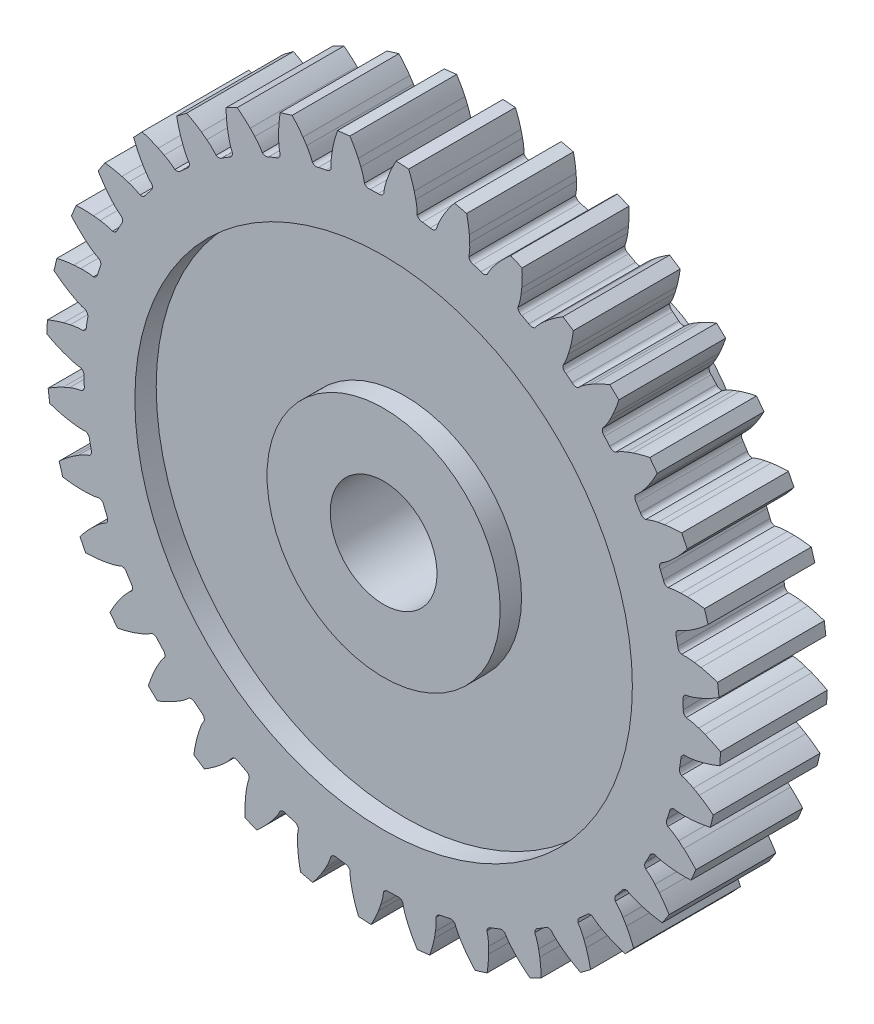
SolidWorks part; units mm, degrees
ref_plane "Front Plane" through (0, 0, 0) normal (0, 0, 1) x (1, 0, 0)
ref_plane "Top Plane" through (0, 0, 0) normal (0, 1, 0) x (1, 0, 0)
ref_plane "Right Plane" through (0, 0, 0) normal (1, 0, 0) x (0, 0, -1)
sketch "Model" plane through (0, 0, 0) normal (0, 0, 1) x (1, 0, 0)
  line L0 (77.4091, 88.3835) -> (77.6633, 88.6903)
  line L1 (78.392, 89.4098) -> (79.0739, 89.1177)
  line L2 (79.0555, 88.0937) -> (79.0087, 87.6981)
  line L3 (79.0512, 86.6569) -> (79.4656, 86.4348)
  line L4 (80.3562, 86.9756) -> (80.6598, 87.2336)
  line L5 (81.5024, 87.8157) -> (82.1232, 87.4096)
  line L6 (81.9273, 86.4044) -> (81.8124, 86.0229)
  line L7 (81.6735, 84.9902) -> (82.0431, 84.6994)
  line L8 (83.0141, 85.0774) -> (83.3578, 85.2788)
  line L9 (84.2887, 85.7057) -> (84.8295, 85.198)
  line L10 (84.462, 84.242) -> (84.2827, 83.8863)
  line L11 (83.9666, 82.8934) -> (84.28, 82.5429)
  line L12 (85.3019, 82.7465) -> (85.6754, 82.8851)
  line L13 (86.6663, 83.144) -> (87.1107, 82.55)
  line L14 (86.5828, 81.6724) -> (86.3444, 81.3532)
  line L15 (85.8607, 80.4303) -> (86.1085, 80.0307)
  line L16 (87.1503, 80.0538) -> (87.5422, 80.1254)
  line L17 (88.5629, 80.2082) -> (88.8975, 79.5461)
  line L18 (88.2252, 78.7735) -> (87.935, 78.5006)
  line L19 (87.2984, 77.6757) -> (87.473, 77.2391)
  line L20 (88.5029, 77.0809) -> (88.9013, 77.0835)
  line L21 (89.921, 76.9878) -> (90.1354, 76.2776)
  line L22 (89.3392, 75.6335) -> (89.006, 75.4151)
  line L23 (88.2358, 74.7133) -> (88.332, 74.253)
  line L24 (89.3188, 73.9184) -> (89.7116, 73.8517)
  line L25 (90.6991, 73.5804) -> (90.787, 72.8438)
  line L26 (89.891, 72.3477) -> (89.525, 72.1905)
  line L27 (88.6446, 71.6331) -> (88.6594, 71.1631)
  line L28 (89.5731, 70.6623) -> (89.9484, 70.5284)
  line L29 (90.8738, 70.0897) -> (90.8324, 69.349)
  line L30 (89.8639, 69.0161) -> (89.4761, 68.9248)
  line L31 (88.5123, 68.5287) -> (88.4453, 68.0633)
  line L32 (89.2582, 67.4114) -> (89.6044, 67.2144)
  line L33 (90.4396, 66.6217) -> (90.2703, 65.8994)
  line L34 (89.2587, 65.7397) -> (88.8609, 65.7172)
  line L35 (87.843, 65.4945) -> (87.6962, 65.0478)
  line L36 (88.3835, 64.2646) -> (88.6903, 64.0105)
  line L37 (89.4099, 63.2817) -> (89.1177, 62.5999)
  line L38 (88.0937, 62.6183) -> (87.6981, 62.6651)
  line L39 (86.6569, 62.6226) -> (86.4348, 62.2082)
  line L40 (86.9756, 61.3175) -> (87.2336, 61.014)
  line L41 (87.8157, 60.1714) -> (87.4096, 59.5506)
  line L42 (86.4044, 59.7465) -> (86.0229, 59.8614)
  line L43 (84.9902, 60.0002) -> (84.6995, 59.6307)
  line L44 (85.0774, 58.6597) -> (85.2788, 58.3159)
  line L45 (85.7058, 57.385) -> (85.198, 56.8442)
  line L46 (84.2421, 57.2117) -> (83.8863, 57.3911)
  line L47 (82.8934, 57.7072) -> (82.5429, 57.3938)
  line L48 (82.7465, 56.3719) -> (82.8852, 55.9983)
  line L49 (83.144, 55.0075) -> (82.55, 54.563)
  line L50 (81.6724, 55.0909) -> (81.3532, 55.3293)
  line L51 (80.4303, 55.8131) -> (80.0307, 55.5653)
  line L52 (80.0538, 54.5235) -> (80.1254, 54.1316)
  line L53 (80.2082, 53.1108) -> (79.5461, 52.7763)
  line L54 (78.7735, 53.4486) -> (78.5006, 53.7388)
  line L55 (77.6757, 54.3754) -> (77.2391, 54.2008)
  line L56 (77.081, 53.1709) -> (77.0835, 52.7725)
  line L57 (76.9878, 51.7528) -> (76.2776, 51.5383)
  line L58 (75.6335, 52.3346) -> (75.4151, 52.6678)
  line L59 (74.7133, 53.438) -> (74.253, 53.3418)
  line L60 (73.9184, 52.355) -> (73.8517, 51.9622)
  line L61 (73.5804, 50.9746) -> (72.8438, 50.8868)
  line L62 (72.3478, 51.7827) -> (72.1905, 52.1488)
  line L63 (71.6331, 53.0292) -> (71.1632, 53.0144)
  line L64 (70.6623, 52.1006) -> (70.5284, 51.7254)
  line L65 (70.0897, 50.8) -> (69.349, 50.8413)
  line L66 (69.0161, 51.8098) -> (68.9248, 52.1977)
  line L67 (68.5287, 53.1614) -> (68.0633, 53.2285)
  line L68 (67.4114, 52.4156) -> (67.2144, 52.0693)
  line L69 (66.6217, 51.2341) -> (65.8994, 51.4035)
  line L70 (65.7397, 52.4151) -> (65.7172, 52.8129)
  line L71 (65.4945, 53.8308) -> (65.0478, 53.9776)
  line L72 (64.2646, 53.2903) -> (64.0105, 52.9835)
  line L73 (63.2817, 52.2639) -> (62.5999, 52.5561)
  line L74 (62.6183, 53.5801) -> (62.6651, 53.9757)
  line L75 (62.6226, 55.0168) -> (62.2082, 55.239)
  line L76 (61.3175, 54.6981) -> (61.014, 54.4401)
  line L77 (60.1714, 53.858) -> (59.5506, 54.2642)
  line L78 (59.7465, 55.2694) -> (59.8614, 55.6509)
  line L79 (60.0002, 56.6836) -> (59.6307, 56.9743)
  line L80 (58.6597, 56.5963) -> (58.3159, 56.395)
  line L81 (57.385, 55.968) -> (56.8442, 56.4758)
  line L82 (57.2117, 57.4317) -> (57.3911, 57.7875)
  line L83 (57.7072, 58.7804) -> (57.3938, 59.1308)
  line L84 (56.3719, 58.9272) -> (55.9983, 58.7886)
  line L85 (55.0075, 58.5298) -> (54.563, 59.1238)
  line L86 (55.0909, 60.0013) -> (55.3293, 60.3206)
  line L87 (55.8131, 61.2435) -> (55.5653, 61.6431)
  line L88 (54.5235, 61.62) -> (54.1316, 61.5483)
  line L89 (53.1108, 61.4655) -> (52.7763, 62.1276)
  line L90 (53.4486, 62.9002) -> (53.7388, 63.1732)
  line L91 (54.3754, 63.9981) -> (54.2008, 64.4346)
  line L92 (53.1709, 64.5928) -> (52.7725, 64.5903)
  line L93 (51.7528, 64.686) -> (51.5384, 65.3961)
  line L94 (52.3346, 66.0402) -> (52.6678, 66.2587)
  line L95 (53.438, 66.9605) -> (53.3418, 67.4207)
  line L96 (52.355, 67.7553) -> (51.9622, 67.822)
  line L97 (50.9747, 68.0933) -> (50.8868, 68.83)
  line L98 (51.7827, 69.326) -> (52.1488, 69.4833)
  line L99 (53.0292, 70.0407) -> (53.0144, 70.5106)
  line L100 (52.1007, 71.0115) -> (51.7254, 71.1454)
  line L101 (50.8, 71.5841) -> (50.8414, 72.3247)
  line L102 (51.8098, 72.6577) -> (52.1977, 72.749)
  line L103 (53.1614, 73.145) -> (53.2285, 73.6104)
  line L104 (52.4156, 74.2624) -> (52.0693, 74.4594)
  line L105 (51.2342, 75.0521) -> (51.4035, 75.7743)
  line L106 (52.4151, 75.934) -> (52.8129, 75.9566)
  line L107 (53.8308, 76.1793) -> (53.9776, 76.626)
  line L108 (53.2903, 77.4091) -> (52.9835, 77.6633)
  line L109 (52.2639, 78.392) -> (52.5561, 79.0739)
  line L110 (53.5801, 79.0555) -> (53.9757, 79.0086)
  line L111 (55.0168, 79.0512) -> (55.239, 79.4656)
  line L112 (54.6981, 80.3562) -> (54.4401, 80.6598)
  line L113 (53.858, 81.5024) -> (54.2642, 82.1232)
  line L114 (55.2694, 81.9272) -> (55.6509, 81.8124)
  line L115 (56.6836, 81.6735) -> (56.9743, 82.043)
  line L116 (56.5963, 83.0141) -> (56.395, 83.3578)
  line L117 (55.968, 84.2887) -> (56.4758, 84.8295)
  line L118 (57.4317, 84.462) -> (57.7875, 84.2827)
  line L119 (58.7804, 83.9666) -> (59.1309, 84.28)
  line L120 (58.9272, 85.3019) -> (58.7886, 85.6754)
  line L121 (58.5298, 86.6663) -> (59.1238, 87.1107)
  line L122 (60.0014, 86.5828) -> (60.3206, 86.3444)
  line L123 (61.2435, 85.8607) -> (61.6431, 86.1085)
  line L124 (61.62, 87.1502) -> (61.5483, 87.5422)
  line L125 (61.4655, 88.5629) -> (62.1277, 88.8974)
  line L126 (62.9002, 88.2252) -> (63.1732, 87.935)
  line L127 (63.9981, 87.2983) -> (64.4346, 87.473)
  line L128 (64.5928, 88.5029) -> (64.5903, 88.9013)
  line L129 (64.686, 89.9209) -> (65.3962, 90.1354)
  line L130 (66.0402, 89.3392) -> (66.2587, 89.006)
  line L131 (66.9605, 88.2358) -> (67.4207, 88.332)
  line L132 (67.7553, 89.3188) -> (67.8221, 89.7116)
  line L133 (68.0934, 90.6991) -> (68.83, 90.787)
  line L134 (69.326, 89.891) -> (69.4833, 89.525)
  line L135 (70.0407, 88.6446) -> (70.5106, 88.6594)
  line L136 (71.0115, 89.5731) -> (71.1454, 89.9483)
  line L137 (71.5841, 90.8738) -> (72.3248, 90.8324)
  line L138 (72.6577, 89.8639) -> (72.749, 89.4761)
  line L139 (73.1451, 88.5123) -> (73.6104, 88.4453)
  line L140 (74.2624, 89.2581) -> (74.4594, 89.6044)
  line L141 (75.0521, 90.4396) -> (75.7743, 90.2703)
  line L142 (75.934, 89.2587) -> (75.9566, 88.8609)
  line L143 (76.1793, 87.843) -> (76.626, 87.6962)
  circle A0 centre (70.8369, 70.8369) radius 3.175
  arc A1 (76.626, 87.6962) -> (76.9961, 87.7414) centre (76.7799, 87.9735) ccw
  arc A2 (77.4091, 88.3835) -> (76.9961, 87.7414) centre (79.8839, 86.3375) ccw
  arc A3 (78.392, 89.4098) -> (77.6633, 88.6903) centre (83.4985, 83.5097) ccw
  arc A4 (79.0555, 88.0937) -> (79.0739, 89.1177) centre (71.2797, 88.7455) ccw
  arc A5 (78.8287, 86.9562) -> (79.0087, 87.6981) centre (75.8203, 88.0788) ccw
  arc A6 (78.8287, 86.9562) -> (79.0512, 86.6569) centre (79.1459, 86.9597) ccw
  arc A7 (79.4656, 86.4348) -> (79.838, 86.4151) centre (79.6654, 86.6812) ccw
  arc A8 (80.3562, 86.9756) -> (79.838, 86.4151) centre (82.4381, 84.531) ccw
  arc A9 (81.5024, 87.8157) -> (80.6598, 87.2336) centre (85.5068, 81.1185) ccw
  arc A10 (81.9273, 86.4044) -> (82.1232, 87.4096) centre (74.3828, 88.3966) ccw
  arc A11 (81.5063, 85.3235) -> (81.8124, 86.0229) centre (78.7386, 86.9515) ccw
  arc A12 (81.5063, 85.3235) -> (81.6735, 84.9902) centre (81.8193, 85.2719) ccw
  arc A13 (82.0431, 84.6994) -> (82.4064, 84.6154) centre (82.2826, 84.9074) ccw
  arc A14 (83.0141, 85.0774) -> (82.4064, 84.6154) centre (84.6399, 82.3084) ccw
  arc A15 (84.2887, 85.7057) -> (83.3578, 85.2788) centre (87.0693, 78.4149) ccw
  arc A16 (84.462, 84.242) -> (84.8295, 85.198) centre (77.3781, 87.5141) ccw
  arc A17 (83.8598, 83.2507) -> (84.2827, 83.8863) centre (81.4169, 85.3345) ccw
  arc A18 (83.8598, 83.2507) -> (83.9666, 82.8934) centre (84.1591, 83.1455) ccw
  arc A19 (84.28, 82.5429) -> (84.6232, 82.397) centre (84.552, 82.7062) ccw
  arc A20 (85.3019, 82.7465) -> (84.6232, 82.397) centre (86.4222, 79.7373) ccw
  arc A21 (86.6663, 83.144) -> (85.6754, 82.8851) centre (88.1386, 75.481) ccw
  arc A22 (86.5828, 81.6724) -> (87.1107, 82.55) centre (80.1747, 86.1248) ccw
  arc A23 (85.8176, 80.8007) -> (86.3444, 81.3532) centre (83.7736, 83.2771) ccw
  arc A24 (85.8176, 80.8007) -> (85.8607, 80.4303) centre (86.0941, 80.6451) ccw
  arc A25 (86.1085, 80.0307) -> (86.4212, 79.8274) centre (86.4047, 80.1442) ccw
  arc A26 (87.1503, 80.0538) -> (86.4212, 79.8274) centre (87.7309, 76.8957) ccw
  arc A27 (88.5629, 80.2082) -> (87.5422, 80.1254) centre (88.6822, 72.4061) ccw
  arc A28 (88.2252, 78.7735) -> (88.8975, 79.5461) centre (82.6876, 84.2711) ccw
  arc A29 (87.3202, 78.0479) -> (87.935, 78.5006) centre (85.7373, 80.8417) ccw
  arc A30 (87.3202, 78.0479) -> (87.2984, 77.6757) centre (87.5655, 77.8467) ccw
  arc A31 (87.473, 77.2391) -> (87.7456, 76.9847) centre (87.7844, 77.2995) ccw
  arc A32 (88.5029, 77.0809) -> (87.7456, 76.9847) centre (88.5264, 73.87) ccw
  arc A33 (89.921, 76.9878) -> (88.9013, 77.0835) centre (88.6835, 69.2834) ccw
  arc A34 (89.3392, 75.6335) -> (90.1354, 76.2776) centre (84.8404, 82.0091) ccw
  arc A35 (88.322, 75.0761) -> (89.006, 75.4151) centre (87.2483, 78.1022) ccw
  arc A36 (88.322, 75.0761) -> (88.2358, 74.7133) centre (88.5286, 74.8354) ccw
  arc A37 (88.332, 74.253) -> (88.5563, 73.9551) centre (88.6492, 74.2584) ccw
  arc A38 (89.3188, 73.9184) -> (88.5563, 73.9551) centre (88.7844, 70.7522) ccw
  arc A39 (90.6991, 73.5804) -> (89.7116, 73.8517) centre (88.1427, 66.208) ccw
  arc A40 (89.891, 72.3477) -> (90.787, 72.8438) centre (86.5677, 79.4077) ccw
  arc A41 (88.7925, 71.9754) -> (89.525, 72.1905) centre (88.2606, 75.142) ccw
  arc A42 (88.7925, 71.9754) -> (88.6446, 71.6331) centre (88.9542, 71.7025) ccw
  arc A43 (88.6594, 71.1631) -> (88.8286, 70.8308) centre (88.9727, 71.1134) ccw
  arc A44 (89.5731, 70.6623) -> (88.8286, 70.8308) centre (88.497, 67.637) ccw
  arc A45 (90.8738, 70.0897) -> (89.9484, 70.5284) centre (87.0759, 63.2732) ccw
  arc A46 (89.8639, 69.0161) -> (90.8324, 69.349) centre (87.817, 76.5459) ccw
  arc A47 (88.7174, 68.8402) -> (89.4761, 68.9248) centre (88.7434, 72.0511) ccw
  arc A48 (88.7174, 68.8402) -> (88.5123, 68.5287) centre (88.8292, 68.5433) ccw
  arc A49 (88.4453, 68.0633) -> (88.5542, 67.7067) centre (88.7452, 67.9599) ccw
  arc A50 (89.2582, 67.4114) -> (88.5542, 67.7067) centre (87.673, 64.6189) ccw
  arc A51 (90.4396, 66.6217) -> (89.6044, 67.2144) centre (85.5158, 60.5682) ccw
  arc A52 (89.2587, 65.7397) -> (90.2703, 65.8994) centre (88.5504, 73.5106) ccw
  arc A53 (88.0991, 65.7656) -> (88.8609, 65.7172) centre (88.6822, 68.9232) ccw
  arc A54 (88.0991, 65.7656) -> (87.843, 65.4945) centre (88.1576, 65.4538) ccw
  arc A55 (87.6962, 65.0478) -> (87.7414, 64.6777) centre (87.9736, 64.8939) ccw
  arc A56 (88.3835, 64.2646) -> (87.7414, 64.6777) centre (86.3375, 61.7898) ccw
  arc A57 (89.4099, 63.2817) -> (88.6903, 64.0105) centre (83.5097, 58.1753) ccw
  arc A58 (88.0937, 62.6183) -> (89.1177, 62.5999) centre (88.7455, 70.3941) ccw
  arc A59 (86.9562, 62.8451) -> (87.6981, 62.6651) centre (88.0788, 65.8535) ccw
  arc A60 (86.9562, 62.8451) -> (86.6569, 62.6226) centre (86.9597, 62.5279) ccw
  arc A61 (86.4348, 62.2082) -> (86.4151, 61.8358) centre (86.6812, 62.0084) ccw
  arc A62 (86.9756, 61.3175) -> (86.4151, 61.8358) centre (84.531, 59.2356) ccw
  arc A63 (87.8157, 60.1714) -> (87.2336, 61.014) centre (81.1185, 56.167) ccw
  arc A64 (86.4044, 59.7465) -> (87.4096, 59.5506) centre (88.3966, 67.291) ccw
  arc A65 (85.3235, 60.1674) -> (86.0229, 59.8614) centre (86.9515, 62.9351) ccw
  arc A66 (85.3235, 60.1674) -> (84.9902, 60.0002) centre (85.2719, 59.8544) ccw
  arc A67 (84.6995, 59.6307) -> (84.6154, 59.2674) centre (84.9075, 59.3912) ccw
  arc A68 (85.0774, 58.6597) -> (84.6154, 59.2674) centre (82.3085, 57.0339) ccw
  arc A69 (85.7058, 57.385) -> (85.2788, 58.3159) centre (78.4149, 54.6045) ccw
  arc A70 (84.2421, 57.2117) -> (85.198, 56.8442) centre (87.5141, 64.2957) ccw
  arc A71 (83.2507, 57.8139) -> (83.8863, 57.3911) centre (85.3346, 60.2569) ccw
  arc A72 (83.2507, 57.8139) -> (82.8934, 57.7072) centre (83.1455, 57.5147) ccw
  arc A73 (82.5429, 57.3938) -> (82.3971, 57.0506) centre (82.7062, 57.1218) ccw
  arc A74 (82.7465, 56.3719) -> (82.3971, 57.0506) centre (79.7373, 55.2516) ccw
  arc A75 (83.144, 55.0075) -> (82.8852, 55.9983) centre (75.481, 53.5352) ccw
  arc A76 (81.6724, 55.0909) -> (82.55, 54.563) centre (86.1248, 61.4991) ccw
  arc A77 (80.8007, 55.8562) -> (81.3532, 55.3293) centre (83.2771, 57.9001) ccw
  arc A78 (80.8007, 55.8562) -> (80.4303, 55.8131) centre (80.6452, 55.5797) ccw
  arc A79 (80.0307, 55.5653) -> (79.8275, 55.2526) centre (80.1442, 55.2691) ccw
  arc A80 (80.0538, 54.5235) -> (79.8275, 55.2526) centre (76.8957, 53.9428) ccw
  arc A81 (80.2082, 53.1108) -> (80.1254, 54.1316) centre (72.4061, 52.9916) ccw
  arc A82 (78.7735, 53.4486) -> (79.5461, 52.7763) centre (84.2711, 58.9862) ccw
  arc A83 (78.048, 54.3535) -> (78.5006, 53.7388) centre (80.8417, 55.9365) ccw
  arc A84 (78.048, 54.3535) -> (77.6757, 54.3754) centre (77.8468, 54.1083) ccw
  arc A85 (77.2391, 54.2008) -> (76.9847, 53.9282) centre (77.2995, 53.8894) ccw
  arc A86 (77.081, 53.1709) -> (76.9847, 53.9282) centre (73.8701, 53.1474) ccw
  arc A87 (76.9878, 51.7528) -> (77.0835, 52.7725) centre (69.2834, 52.9902) ccw
  arc A88 (75.6335, 52.3346) -> (76.2776, 51.5383) centre (82.0091, 56.8334) ccw
  arc A89 (75.0761, 53.3518) -> (75.4151, 52.6678) centre (78.1022, 54.4255) ccw
  arc A90 (75.0761, 53.3518) -> (74.7133, 53.438) centre (74.8354, 53.1452) ccw
  arc A91 (74.253, 53.3418) -> (73.9551, 53.1175) centre (74.2584, 53.0246) ccw
  arc A92 (73.9184, 52.355) -> (73.9551, 53.1175) centre (70.7522, 52.8894) ccw
  arc A93 (73.5804, 50.9746) -> (73.8517, 51.9622) centre (66.208, 53.5311) ccw
  arc A94 (72.3478, 51.7827) -> (72.8438, 50.8868) centre (79.4077, 55.1061) ccw
  arc A95 (71.9754, 52.8813) -> (72.1905, 52.1488) centre (75.1421, 53.4132) ccw
  arc A96 (71.9754, 52.8813) -> (71.6331, 53.0292) centre (71.7025, 52.7196) ccw
  arc A97 (71.1632, 53.0144) -> (70.8308, 52.8452) centre (71.1134, 52.7011) ccw
  arc A98 (70.6623, 52.1006) -> (70.8308, 52.8452) centre (67.637, 53.1768) ccw
  arc A99 (70.0897, 50.8) -> (70.5284, 51.7254) centre (63.2732, 54.5978) ccw
  arc A100 (69.0161, 51.8098) -> (69.349, 50.8413) centre (76.5459, 53.8568) ccw
  arc A101 (68.8402, 52.9563) -> (68.9248, 52.1977) centre (72.0511, 52.9303) ccw
  arc A102 (68.8402, 52.9563) -> (68.5287, 53.1614) centre (68.5433, 52.8445) ccw
  arc A103 (68.0633, 53.2285) -> (67.7067, 53.1196) centre (67.9599, 52.9286) ccw
  arc A104 (67.4114, 52.4156) -> (67.7067, 53.1196) centre (64.6189, 54.0007) ccw
  arc A105 (66.6217, 51.2341) -> (67.2144, 52.0693) centre (60.5682, 56.1579) ccw
  arc A106 (65.7397, 52.4151) -> (65.8994, 51.4035) centre (73.5106, 53.1234) ccw
  arc A107 (65.7656, 53.5747) -> (65.7172, 52.8129) centre (68.9232, 52.9915) ccw
  arc A108 (65.7656, 53.5747) -> (65.4945, 53.8308) centre (65.4538, 53.5162) ccw
  arc A109 (65.0478, 53.9776) -> (64.6777, 53.9323) centre (64.8939, 53.7002) ccw
  arc A110 (64.2646, 53.2903) -> (64.6777, 53.9323) centre (61.7898, 55.3363) ccw
  arc A111 (63.2817, 52.2639) -> (64.0105, 52.9835) centre (58.1753, 58.1641) ccw
  arc A112 (62.6183, 53.5801) -> (62.5999, 52.5561) centre (70.3941, 52.9282) ccw
  arc A113 (62.8451, 54.7176) -> (62.6651, 53.9757) centre (65.8535, 53.595) ccw
  arc A114 (62.8451, 54.7176) -> (62.6226, 55.0168) centre (62.5279, 54.7141) ccw
  arc A115 (62.2082, 55.239) -> (61.8358, 55.2587) centre (62.0084, 54.9925) ccw
  arc A116 (61.3175, 54.6981) -> (61.8358, 55.2587) centre (59.2356, 57.1427) ccw
  arc A117 (60.1714, 53.858) -> (61.014, 54.4401) centre (56.167, 60.5553) ccw
  arc A118 (59.7465, 55.2694) -> (59.5506, 54.2642) centre (67.291, 53.2772) ccw
  arc A119 (60.1674, 56.3502) -> (59.8614, 55.6509) centre (62.9351, 54.7223) ccw
  arc A120 (60.1674, 56.3502) -> (60.0002, 56.6836) centre (59.8544, 56.4018) ccw
  arc A121 (59.6307, 56.9743) -> (59.2674, 57.0584) centre (59.3912, 56.7663) ccw
  arc A122 (58.6597, 56.5963) -> (59.2674, 57.0584) centre (57.0339, 59.3653) ccw
  arc A123 (57.385, 55.968) -> (58.3159, 56.395) centre (54.6045, 63.2589) ccw
  arc A124 (57.2117, 57.4317) -> (56.8442, 56.4758) centre (64.2957, 54.1597) ccw
  arc A125 (57.8139, 58.423) -> (57.3911, 57.7875) centre (60.2569, 56.3392) ccw
  arc A126 (57.8139, 58.423) -> (57.7072, 58.7804) centre (57.5147, 58.5282) ccw
  arc A127 (57.3938, 59.1308) -> (57.0506, 59.2767) centre (57.1218, 58.9676) ccw
  arc A128 (56.3719, 58.9272) -> (57.0506, 59.2767) centre (55.2516, 61.9365) ccw
  arc A129 (55.0075, 58.5298) -> (55.9983, 58.7886) centre (53.5352, 66.1927) ccw
  arc A130 (55.0909, 60.0013) -> (54.563, 59.1238) centre (61.4991, 55.5489) ccw
  arc A131 (55.8562, 60.873) -> (55.3293, 60.3206) centre (57.9001, 58.3967) ccw
  arc A132 (55.8562, 60.873) -> (55.8131, 61.2435) centre (55.5797, 61.0286) ccw
  arc A133 (55.5653, 61.6431) -> (55.2526, 61.8463) centre (55.2691, 61.5295) ccw
  arc A134 (54.5235, 61.62) -> (55.2526, 61.8463) centre (53.9428, 64.778) ccw
  arc A135 (53.1108, 61.4655) -> (54.1316, 61.5483) centre (52.9916, 69.2677) ccw
  arc A136 (53.4486, 62.9002) -> (52.7763, 62.1276) centre (58.9862, 57.4027) ccw
  arc A137 (54.3535, 63.6258) -> (53.7388, 63.1732) centre (55.9365, 60.8321) ccw
  arc A138 (54.3535, 63.6258) -> (54.3754, 63.9981) centre (54.1083, 63.827) ccw
  arc A139 (54.2008, 64.4346) -> (53.9282, 64.6891) centre (53.8894, 64.3742) ccw
  arc A140 (53.1709, 64.5928) -> (53.9282, 64.6891) centre (53.1474, 67.8037) ccw
  arc A141 (51.7528, 64.686) -> (52.7725, 64.5903) centre (52.9902, 72.3903) ccw
  arc A142 (52.3346, 66.0402) -> (51.5384, 65.3961) centre (56.8334, 59.6646) ccw
  arc A143 (53.3518, 66.5977) -> (52.6678, 66.2587) centre (54.4255, 63.5715) ccw
  arc A144 (53.3518, 66.5977) -> (53.438, 66.9605) centre (53.1452, 66.8384) ccw
  arc A145 (53.3418, 67.4207) -> (53.1175, 67.7187) centre (53.0246, 67.4153) ccw
  arc A146 (52.355, 67.7553) -> (53.1175, 67.7187) centre (52.8894, 70.9215) ccw
  arc A147 (50.9747, 68.0933) -> (51.9622, 67.822) centre (53.5311, 75.4658) ccw
  arc A148 (51.7827, 69.326) -> (50.8868, 68.83) centre (55.1061, 62.266) ccw
  arc A149 (52.8813, 69.6983) -> (52.1488, 69.4833) centre (53.4132, 66.5317) ccw
  arc A150 (52.8813, 69.6983) -> (53.0292, 70.0407) centre (52.7196, 69.9713) ccw
  arc A151 (53.0144, 70.5106) -> (52.8452, 70.843) centre (52.7011, 70.5604) ccw
  arc A152 (52.1007, 71.0115) -> (52.8452, 70.843) centre (53.1768, 74.0368) ccw
  arc A153 (50.8, 71.5841) -> (51.7254, 71.1454) centre (54.5978, 78.4006) ccw
  arc A154 (51.8098, 72.6577) -> (50.8414, 72.3247) centre (53.8568, 65.1279) ccw
  arc A155 (52.9564, 72.8336) -> (52.1977, 72.749) centre (52.9303, 69.6227) ccw
  arc A156 (52.9564, 72.8336) -> (53.1614, 73.145) centre (52.8446, 73.1304) ccw
  arc A157 (53.2285, 73.6104) -> (53.1196, 73.9671) centre (52.9286, 73.7138) ccw
  arc A158 (52.4156, 74.2624) -> (53.1196, 73.9671) centre (54.0007, 77.0548) ccw
  arc A159 (51.2342, 75.0521) -> (52.0693, 74.4594) centre (56.158, 81.1055) ccw
  arc A160 (52.4151, 75.934) -> (51.4035, 75.7743) centre (53.1234, 68.1632) ccw
  arc A161 (53.5747, 75.9082) -> (52.8129, 75.9566) centre (52.9915, 72.7506) ccw
  arc A162 (53.5747, 75.9082) -> (53.8308, 76.1793) centre (53.5162, 76.2199) ccw
  arc A163 (53.9776, 76.626) -> (53.9323, 76.9961) centre (53.7002, 76.7799) ccw
  arc A164 (53.2903, 77.4091) -> (53.9323, 76.9961) centre (55.3363, 79.8839) ccw
  arc A165 (52.2639, 78.392) -> (52.9835, 77.6633) centre (58.1641, 83.4985) ccw
  arc A166 (53.5801, 79.0555) -> (52.5561, 79.0739) centre (52.9282, 71.2797) ccw
  arc A167 (54.7176, 78.8287) -> (53.9757, 79.0086) centre (53.595, 75.8203) ccw
  arc A168 (54.7176, 78.8287) -> (55.0168, 79.0512) centre (54.7141, 79.1459) ccw
  arc A169 (55.239, 79.4656) -> (55.2587, 79.838) centre (54.9926, 79.6653) ccw
  arc A170 (54.6981, 80.3562) -> (55.2587, 79.838) centre (57.1427, 82.4381) ccw
  arc A171 (53.858, 81.5024) -> (54.4401, 80.6598) centre (60.5553, 85.5067) ccw
  arc A172 (55.2694, 81.9272) -> (54.2642, 82.1232) centre (53.2772, 74.3828) ccw
  arc A173 (56.3502, 81.5063) -> (55.6509, 81.8124) centre (54.7223, 78.7386) ccw
  arc A174 (56.3502, 81.5063) -> (56.6836, 81.6735) centre (56.4019, 81.8193) ccw
  arc A175 (56.9743, 82.043) -> (57.0584, 82.4064) centre (56.7663, 82.2826) ccw
  arc A176 (56.5963, 83.0141) -> (57.0584, 82.4064) centre (59.3653, 84.6398) ccw
  arc A177 (55.968, 84.2887) -> (56.395, 83.3578) centre (63.2589, 87.0692) ccw
  arc A178 (57.4317, 84.462) -> (56.4758, 84.8295) centre (54.1597, 77.3781) ccw
  arc A179 (58.4231, 83.8598) -> (57.7875, 84.2827) centre (56.3392, 81.4169) ccw
  arc A180 (58.4231, 83.8598) -> (58.7804, 83.9666) centre (58.5282, 84.1591) ccw
  arc A181 (59.1309, 84.28) -> (59.2767, 84.6232) centre (58.9676, 84.552) ccw
  arc A182 (58.9272, 85.3019) -> (59.2767, 84.6232) centre (61.9365, 86.4222) ccw
  arc A183 (58.5298, 86.6663) -> (58.7886, 85.6754) centre (66.1927, 88.1386) ccw
  arc A184 (60.0014, 86.5828) -> (59.1238, 87.1107) centre (55.5489, 80.1747) ccw
  arc A185 (60.8731, 85.8176) -> (60.3206, 86.3444) centre (58.3967, 83.7736) ccw
  arc A186 (60.8731, 85.8176) -> (61.2435, 85.8607) centre (61.0286, 86.0941) ccw
  arc A187 (61.6431, 86.1085) -> (61.8463, 86.4212) centre (61.5295, 86.4047) ccw
  arc A188 (61.62, 87.1502) -> (61.8463, 86.4212) centre (64.778, 87.7309) ccw
  arc A189 (61.4655, 88.5629) -> (61.5483, 87.5422) centre (69.2677, 88.6821) ccw
  arc A190 (62.9002, 88.2252) -> (62.1277, 88.8974) centre (57.4027, 82.6875) ccw
  arc A191 (63.6258, 87.3202) -> (63.1732, 87.935) centre (60.8321, 85.7373) ccw
  arc A192 (63.6258, 87.3202) -> (63.9981, 87.2983) centre (63.827, 87.5655) ccw
  arc A193 (64.4346, 87.473) -> (64.6891, 87.7456) centre (64.3743, 87.7844) ccw
  arc A194 (64.5928, 88.5029) -> (64.6891, 87.7456) centre (67.8037, 88.5264) ccw
  arc A195 (64.686, 89.9209) -> (64.5903, 88.9013) centre (72.3903, 88.6835) ccw
  arc A196 (66.0402, 89.3392) -> (65.3962, 90.1354) centre (59.6646, 84.8403) ccw
  arc A197 (66.5977, 88.322) -> (66.2587, 89.006) centre (63.5715, 87.2482) ccw
  arc A198 (66.5977, 88.322) -> (66.9605, 88.2358) centre (66.8384, 88.5286) ccw
  arc A199 (67.4207, 88.332) -> (67.7187, 88.5563) centre (67.4153, 88.6492) ccw
  arc A200 (67.7553, 89.3188) -> (67.7187, 88.5563) centre (70.9215, 88.7843) ccw
  arc A201 (68.0934, 90.6991) -> (67.8221, 89.7116) centre (75.4658, 88.1426) ccw
  arc A202 (69.326, 89.891) -> (68.83, 90.787) centre (62.2661, 86.5676) ccw
  arc A203 (69.6983, 88.7925) -> (69.4833, 89.525) centre (66.5317, 88.2605) ccw
  arc A204 (69.6983, 88.7925) -> (70.0407, 88.6446) centre (69.9713, 88.9541) ccw
  arc A205 (70.5106, 88.6594) -> (70.843, 88.8285) centre (70.5604, 88.9727) ccw
  arc A206 (71.0115, 89.5731) -> (70.843, 88.8285) centre (74.0368, 88.497) ccw
  arc A207 (71.5841, 90.8738) -> (71.1454, 89.9483) centre (78.4006, 87.0759) ccw
  arc A208 (72.6577, 89.8639) -> (72.3248, 90.8324) centre (65.1279, 87.817) ccw
  arc A209 (72.8336, 88.7174) -> (72.749, 89.4761) centre (69.6227, 88.7434) ccw
  arc A210 (72.8336, 88.7174) -> (73.1451, 88.5123) centre (73.1305, 88.8292) ccw
  arc A211 (73.6104, 88.4453) -> (73.9671, 88.5542) centre (73.7139, 88.7452) ccw
  arc A212 (74.2624, 89.2581) -> (73.9671, 88.5542) centre (77.0548, 87.6731) ccw
  arc A213 (75.0521, 90.4396) -> (74.4594, 89.6044) centre (81.1055, 85.5158) ccw
  arc A214 (75.934, 89.2587) -> (75.7743, 90.2703) centre (68.1632, 88.5504) ccw
  arc A215 (75.9082, 88.099) -> (75.9566, 88.8609) centre (72.7506, 88.6822) ccw
  arc A216 (75.9082, 88.099) -> (76.1793, 87.843) centre (76.22, 88.1576) ccw
extrude "Boss-Extrude1" add sketch "Model" along normal blind 6.35
sketch "Sketch2" plane through (0, 0, 6.35) normal (0, 0, 1) x (1, 0, 0)
  line L0 (70.8369, 74.0119) -> (70.8369, -49925.9881) construction
  line L1 (67.6619, 70.8369) -> (50067.6619, 70.8369) construction
  circle A2 centre (70.8369, 70.8369) radius 14.7955
  circle A3 centre (70.8369, 70.8369) radius 6.9342
  dimension "D1" = 29.591
  dimension "D2" = 13.8684
extrude "Cut-Extrude1" cut sketch "Sketch2" against normal blind 1.27
sketch "Sketch3" plane through (0, 0, 0) normal (0, 0, -1) x (-1, 0, 0)
  circle A0 centre (-70.8369, 70.8369) radius 7.62
  circle A1 centre (-70.8369, 70.8369) radius 14.7955
  dimension "D1" = 15.24
extrude "Cut-Extrude2" cut sketch "Sketch3" against normal blind 1.27
sketch "Sketch4" plane through (0, 0, 0) normal (0, 0, -1) x (-1, 0, 0)
  circle A0 centre (-70.8369, 70.8369) radius 7.62
  circle A1 centre (-70.8369, 70.8369) radius 3.175
extrude "Boss-Extrude2" add sketch "Sketch4" along normal blind 7.62
